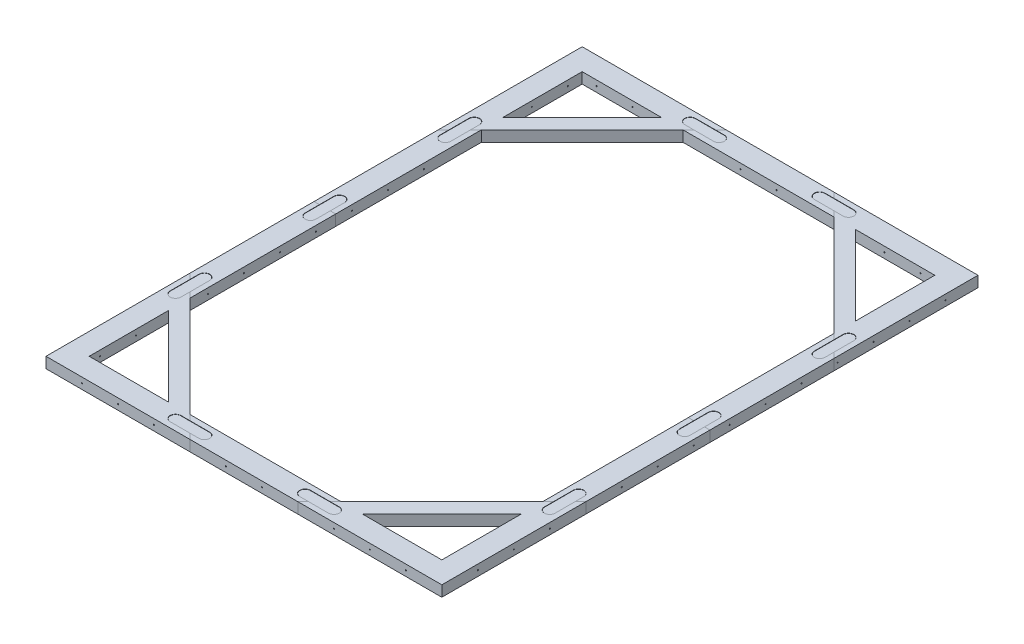
SolidWorks part; units mm, degrees
ref_plane "Front Plane" through (0, 0, 0) normal (0, 0, 1) x (1, 0, 0)
ref_plane "Top Plane" through (0, 0, 0) normal (0, 1, 0) x (1, 0, 0)
ref_plane "Right Plane" through (0, 0, 0) normal (1, 0, 0) x (0, 0, -1)
sketch "Sketch1" plane through (0, 0, 0) normal (0, 1, 0) x (1, 0, 0)
  line L0 (170, 715) -> (30, 575)
  line L1 (0, 0) -> (550, 0)
  line L2 (0, 0) -> (0, 745)
  line L3 (0, 745) -> (550, 745)
  line L4 (550, 0) -> (550, 745)
  line L5 (275, 745) -> (275, 0) construction
  line L6 (0, 372.5) -> (550, 372.5) construction
  line L7 (380, 715) -> (520, 575)
  line L8 (380, 30) -> (520, 170)
  line L9 (170, 30) -> (30, 170)
  line L10 (170, 715) -> (380, 715)
  line L11 (520, 170) -> (520, 575)
  line L12 (170, 30) -> (380, 30)
  line L13 (30, 170) -> (30, 575)
  line L15 (30, 715) -> (520, 715) construction
  line L16 (30, 30) -> (30, 715) construction
  line L17 (30, 30) -> (520, 30) construction
  line L18 (520, 30) -> (520, 715) construction
  dimension "D1" = 550
  dimension "D2" = 745
  dimension "D5" = 30
extrude "Boss-Extrude1" add sketch "Sketch1" along normal blind 15
sketch "Sketch2" plane through (0, 15, 0) normal (0, 1, 0) x (1, 0, 0)
  line L0 (140, 715) -> (30, 715)
  line L1 (30, 715) -> (30, 605)
  line L2 (30, 605) -> (140, 715)
  line L3 (380, 715) -> (170, 715) construction
  line L4 (30, 575) -> (30, 170) construction
  line L5 (170, 715) -> (30, 575) construction
  line L6 (275, 745) -> (275, 545.877) construction
  line L7 (550, 745) -> (0, 745) construction
  line L8 (520, 715) -> (520, 605)
  line L9 (410, 715) -> (520, 715)
  line L10 (520, 605) -> (410, 715)
  line L11 (0, 372.5) -> (324.6432, 372.5) construction
  line L12 (0, 745) -> (0, 0) construction
  line L13 (410, 30) -> (520, 30)
  line L14 (520, 140) -> (410, 30)
  line L15 (520, 30) -> (520, 140)
  line L16 (30, 30) -> (30, 140)
  line L17 (140, 30) -> (30, 30)
  line L18 (30, 140) -> (140, 30)
  dimension "D1" = 30
extrude "Cut-Extrude1" cut sketch "Sketch2" against normal blind 15
sketch "Sketch3" plane through (0, 15, 0) normal (0, 1, 0) x (1, 0, 0)
  line L0 (170, 715) -> (200, 745)
  line L1 (550, 745) -> (0, 745) construction
  line L2 (380, 715) -> (350, 745)
  line L3 (520, 575) -> (380, 715) construction
  line L4 (170, 715) -> (30, 575) construction
  line L5 (30, 575) -> (0, 545)
  line L6 (0, 745) -> (0, 0) construction
  line L7 (520, 575) -> (550, 545)
  line L8 (550, 0) -> (550, 745) construction
  line L9 (30, 170) -> (0, 200)
  line L10 (30, 170) -> (170, 30) construction
  line L11 (170, 30) -> (200, 0)
  line L12 (0, 0) -> (550, 0) construction
  line L13 (520, 170) -> (550, 200)
  line L14 (380, 30) -> (350, 0)
  line L15 (380, 30) -> (520, 170) construction
  line L16 (0, 372.5) -> (30, 372.5)
  line L17 (30, 575) -> (30, 170) construction
  line L18 (520, 372.5) -> (550, 372.5)
  line L19 (520, 170) -> (520, 575) construction
extrude "Cut-Extrude-Thin1" cut sketch "Sketch3" against normal blind 15 thin thin type mid plane wall 0.0001
sketch "Sketch4" plane through (0, 15, 0) normal (0, 1, 0) x (1, 0, 0)
  line L0 (184.9999, 730) -> (365.0001, 730) construction
  line L1 (170, 715) -> (199.9999, 745) construction
  line L2 (380, 715) -> (350.0001, 745) construction
  line L3 (164.9999, 730) -> (204.9999, 730) construction
  line L4 (164.9999, 737.5) -> (204.9999, 737.5)
  line L5 (164.9999, 722.5) -> (204.9999, 722.5)
  line L6 (275, 745) -> (275, 715) construction
  line L7 (350, 745) -> (200, 745) construction
  line L8 (379.9999, 715) -> (170.0001, 715) construction
  line L9 (385.0001, 730) -> (345.0001, 730) construction
  line L10 (385.0001, 737.5) -> (345.0001, 737.5)
  line L11 (385.0001, 722.5) -> (345.0001, 722.5)
  line L12 (0, 372.5) -> (550, 372.5) construction
  line L13 (385.0001, 14.9999) -> (345.0001, 14.9999) construction
  line L14 (385.0001, 7.4999) -> (345.0001, 7.4999)
  line L15 (385.0001, 22.4999) -> (345.0001, 22.4999)
  line L16 (164.9999, 14.9999) -> (204.9999, 14.9999) construction
  line L17 (164.9999, 7.4999) -> (204.9999, 7.4999)
  line L18 (164.9999, 22.4999) -> (204.9999, 22.4999)
  line L19 (15, 580.0001) -> (15, 540.0001) construction
  line L20 (22.5, 580.0001) -> (22.5, 540.0001)
  line L21 (7.5, 580.0001) -> (7.5, 540.0001)
  line L22 (30, 575) -> (0, 545.0001) construction
  line L23 (15, 164.9998) -> (15, 204.9998) construction
  line L24 (22.5, 164.9998) -> (22.5, 204.9998)
  line L25 (7.5, 164.9998) -> (7.5, 204.9998)
  line L26 (535, 580.0001) -> (535, 540.0001) construction
  line L27 (527.5, 580.0001) -> (527.5, 540.0001)
  line L28 (542.5, 580.0001) -> (542.5, 540.0001)
  line L29 (535, 164.9998) -> (535, 204.9998) construction
  line L30 (527.5, 164.9998) -> (527.5, 204.9998)
  line L31 (542.5, 164.9998) -> (542.5, 204.9998)
  line L32 (15, 392.5) -> (15, 352.5) construction
  line L33 (22.5, 392.5) -> (22.5, 352.5)
  line L34 (7.5, 392.5) -> (7.5, 352.5)
  line L35 (535, 392.5) -> (535, 352.5) construction
  line L36 (527.5, 392.5) -> (527.5, 352.5)
  line L37 (542.5, 392.5) -> (542.5, 352.5)
  arc A0 (164.9999, 737.5) -> (164.9999, 722.5) centre (164.9999, 730) ccw
  arc A1 (204.9999, 722.5) -> (204.9999, 737.5) centre (204.9999, 730) ccw
  arc A2 (385.0001, 737.5) -> (385.0001, 722.5) centre (385.0001, 730) cw
  arc A3 (345.0001, 722.5) -> (345.0001, 737.5) centre (345.0001, 730) cw
  arc A4 (385.0001, 7.4999) -> (385.0001, 22.4999) centre (385.0001, 14.9999) ccw
  arc A5 (345.0001, 22.4999) -> (345.0001, 7.4999) centre (345.0001, 14.9999) ccw
  arc A6 (164.9999, 7.4999) -> (164.9999, 22.4999) centre (164.9999, 14.9999) cw
  arc A7 (204.9999, 22.4999) -> (204.9999, 7.4999) centre (204.9999, 14.9999) cw
  arc A8 (22.5, 580.0001) -> (7.5, 580.0001) centre (15, 580.0001) ccw
  arc A9 (7.5, 540.0001) -> (22.5, 540.0001) centre (15, 540.0001) ccw
  arc A10 (22.5, 164.9998) -> (7.5, 164.9998) centre (15, 164.9998) cw
  arc A11 (7.5, 204.9998) -> (22.5, 204.9998) centre (15, 204.9998) cw
  arc A12 (527.5, 580.0001) -> (542.5, 580.0001) centre (535, 580.0001) cw
  arc A13 (542.5, 540.0001) -> (527.5, 540.0001) centre (535, 540.0001) cw
  arc A14 (527.5, 164.9998) -> (542.5, 164.9998) centre (535, 164.9998) ccw
  arc A15 (542.5, 204.9998) -> (527.5, 204.9998) centre (535, 204.9998) ccw
  arc A16 (22.5, 392.5) -> (7.5, 392.5) centre (15, 392.5) ccw
  arc A17 (7.5, 352.5) -> (22.5, 352.5) centre (15, 352.5) ccw
  arc A18 (527.5, 392.5) -> (542.5, 392.5) centre (535, 392.5) cw
  arc A19 (542.5, 352.5) -> (527.5, 352.5) centre (535, 352.5) cw
  point P8 (184.9999, 730)
  point P21 (365.0001, 730)
  point P32 (365.0001, 14.9999)
  point P39 (184.9999, 14.9999)
  point P46 (15, 560.0001)
  point P51 (15, 372.5)
  point P56 (15, 184.9998)
  point P63 (535, 560.0001)
  point P70 (535, 184.9998)
  point P84 (535, 372.5)
  dimension "D1" = 40
  dimension "D2" = 15
  dimension "D3" = 40
  dimension "D4" = 15
  dimension "D5" = 40
  dimension "D6" = 15
extrude "Cut-Extrude2" cut sketch "Sketch4" against normal blind 5
sketch "Sketch5" plane through (0, 10, 0) normal (0, 1, 0) x (1, 0, 0)
  line L20 (177.5, 22.2999) -> (164.9999, 22.2999)
  line L21 (164.9999, 22.2999) -> (204.9999, 22.2999)
  line L26 (164.9999, 7.6999) -> (204.9999, 7.6999)
  line L27 (192.5002, 7.6999) -> (204.9999, 7.6999)
  line L28 (204.9999, 22.2999) -> (177.5002, 22.2999)
  line L29 (7.7, 392.5) -> (7.7, 352.5)
  line L30 (22.3, 392.5) -> (22.3, 352.5)
  line L31 (22.3, 204.9998) -> (22.3, 164.9998)
  line L32 (7.7, 204.9998) -> (7.7, 164.9998)
  line L33 (275, 715) -> (275, 30) construction
  line L34 (379.9999, 715) -> (170.0001, 715) construction
  line L35 (170.0001, 30) -> (379.9999, 30) construction
  line L36 (30, 372.5001) -> (520, 372.5) construction
  line L37 (542.3, 392.5) -> (542.3, 352.5)
  line L38 (527.7, 392.5) -> (527.7, 352.5)
  line L39 (542.3, 204.9998) -> (542.3, 164.9998)
  line L40 (527.7, 204.9998) -> (527.7, 164.9998)
  line L41 (385.0001, 22.2999) -> (345.0001, 22.2999)
  line L42 (385.0001, 7.6999) -> (345.0001, 7.6999)
  line L43 (542.3001, 540) -> (542.3001, 580)
  line L44 (527.7001, 540) -> (527.7001, 580)
  line L45 (7.7001, 540.0003) -> (7.7001, 580.0003)
  line L46 (22.3001, 540.0003) -> (22.3001, 580.0003)
  line L47 (165.0001, 722.7002) -> (205.0001, 722.7001)
  line L48 (165.0001, 737.3002) -> (205.0001, 737.3001)
  line L49 (385.0002, 737.3001) -> (345.0002, 737.3001)
  line L50 (385.0002, 722.7001) -> (345.0002, 722.7001)
  arc A10 (164.9999, 22.2999) -> (164.9999, 7.6999) centre (164.9999, 14.9999) ccw
  arc A11 (164.9999, 22.2999) -> (164.9999, 7.6999) centre (164.9999, 14.9999) ccw
  arc A14 (204.9999, 7.6999) -> (204.9999, 22.2999) centre (204.9999, 14.9999) ccw
  arc A15 (204.9999, 7.6999) -> (204.9999, 22.2999) centre (204.9999, 14.9999) ccw
  arc A17 (22.3, 204.9998) -> (7.7, 204.9998) centre (15, 204.9998) ccw
  arc A18 (22.3, 204.9998) -> (7.7, 204.9998) centre (15, 204.9998) ccw
  arc A20 (7.7, 164.9998) -> (22.3, 164.9998) centre (15, 164.9998) ccw
  arc A21 (7.7, 164.9998) -> (22.3, 164.9998) centre (15, 164.9998) ccw
  arc A23 (22.3, 392.5) -> (7.7, 392.5) centre (15, 392.5) ccw
  arc A24 (22.3, 392.5) -> (7.7, 392.5) centre (15, 392.5) ccw
  arc A25 (542.3, 352.5) -> (527.7, 352.5) centre (535, 352.5) cw
  arc A26 (7.7, 352.5) -> (22.3, 352.5) centre (15, 352.5) ccw
  arc A27 (7.7, 352.5) -> (22.3, 352.5) centre (15, 352.5) ccw
  arc A28 (527.7, 392.5) -> (542.3, 392.5) centre (535, 392.5) cw
  arc A29 (542.3, 164.9998) -> (527.7, 164.9998) centre (535, 164.9998) cw
  arc A30 (527.7, 204.9998) -> (542.3, 204.9998) centre (535, 204.9998) cw
  arc A31 (345.0001, 7.6999) -> (345.0001, 22.2999) centre (345.0001, 14.9999) cw
  arc A32 (385.0001, 22.2999) -> (385.0001, 7.6999) centre (385.0001, 14.9999) cw
  arc A33 (527.7001, 540) -> (542.3001, 540) centre (535.0001, 540) ccw
  arc A34 (542.3001, 580) -> (527.7001, 580) centre (535.0001, 580) ccw
  arc A35 (7.7001, 580.0003) -> (22.3001, 580.0003) centre (15.0001, 580.0003) cw
  arc A36 (22.3001, 540.0003) -> (7.7001, 540.0003) centre (15.0001, 540.0003) cw
  arc A37 (205.0001, 737.3001) -> (205.0001, 722.7001) centre (205.0001, 730.0001) cw
  arc A38 (165.0001, 722.7002) -> (165.0001, 737.3002) centre (165.0001, 730.0002) cw
  arc A39 (385.0002, 722.7001) -> (385.0002, 737.3001) centre (385.0002, 730.0001) ccw
  arc A40 (345.0002, 737.3001) -> (345.0002, 722.7001) centre (345.0002, 730.0001) ccw
  dimension "D1" = 0.2
  dimension "D2" = 0.2
  dimension "D3" = 0.2
  dimension "D4" = 0.2
  dimension "D5" = 0.2
  dimension "D6" = 0.2
extrude "Boss-Extrude2" add sketch "Sketch5" along normal blind 4.8 separate body
sketch "Sketch8" plane through (0, 0, 0) normal (0, 0, 1) x (1, 0, 0)
  line L0 (0, 7.5) -> (550, 7.5) construction
  line L1 (0, 15) -> (0, 0) construction
  line L2 (550, 15) -> (550, 0) construction
  circle A0 centre (50, 7.5) radius 0.75
  circle A1 centre (100, 7.5) radius 0.75
  circle A2 centre (150, 7.5) radius 0.75
  circle A4 centre (250, 7.5) radius 0.75
  circle A5 centre (300, 7.5) radius 0.75
  circle A7 centre (400, 7.5) radius 0.75
  circle A8 centre (450, 7.5) radius 0.75
  circle A9 centre (500, 7.5) radius 0.75
  circle A10 centre (200, 7.5) radius 0.75 [skipped]
  circle A11 centre (350, 7.5) radius 0.75 [skipped]
  dimension "D1" = 1.5
  dimension "D2" = 50
  dimension "D3" = 10
extrude "Cut-Extrude3" cut sketch "Sketch8" against normal up to surface (30 mm away) up to face at (85, 7.5, -30)
sketch "Sketch9" plane through (550, 0, 0) normal (1, 0, 0) x (0, 0, -1)
  line L0 (0, 7.5) -> (745, 7.5) construction
  line L1 (0, 15) -> (0, 0) construction
  line L2 (745, 15) -> (745, 0) construction
  circle A0 centre (50, 7.5) radius 0.75
  circle A1 centre (100, 7.5) radius 0.75
  circle A2 centre (150, 7.5) radius 0.75
  circle A4 centre (250, 7.5) radius 0.75
  circle A5 centre (300, 7.5) radius 0.75
  circle A6 centre (350, 7.5) radius 0.75
  circle A7 centre (400, 7.5) radius 0.75
  circle A8 centre (450, 7.5) radius 0.75
  circle A9 centre (500, 7.5) radius 0.75
  circle A10 centre (550, 7.5) radius 0.75
  circle A11 centre (600, 7.5) radius 0.75
  circle A12 centre (650, 7.5) radius 0.75
  circle A13 centre (700, 7.5) radius 0.75
  circle A14 centre (200, 7.5) radius 0.75 [skipped]
  dimension "D1" = 1.5
  dimension "D2" = 50
  dimension "D3" = 14
extrude "Cut-Extrude4" cut sketch "Sketch9" against normal up to surface (30 mm away) up to face at (520, 7.5, -271.25)
sketch "Sketch10" plane through (0, 0, -745) normal (0, 0, -1) x (-1, 0, 0)
  line L0 (-550, 7.5) -> (0, 7.5) construction
  line L1 (-550, 15) -> (-550, 0) construction
  line L2 (0, 15) -> (0, 0) construction
  circle A0 centre (-500, 7.5) radius 0.75
  circle A1 centre (-450, 7.5) radius 0.75
  circle A2 centre (-400, 7.5) radius 0.75
  circle A4 centre (-300, 7.5) radius 0.75
  circle A5 centre (-250, 7.5) radius 0.75
  circle A7 centre (-150, 7.5) radius 0.75
  circle A8 centre (-100, 7.5) radius 0.75
  circle A9 centre (-50, 7.5) radius 0.75
  circle A10 centre (-350, 7.5) radius 0.75 [skipped]
  circle A11 centre (-200, 7.5) radius 0.75 [skipped]
  dimension "D1" = 1.5
  dimension "D2" = 50
  dimension "D3" = 10
extrude "Cut-Extrude5" cut sketch "Sketch10" against normal up to surface (30 mm away) up to face at (275, 7.5, -715)
sketch "Sketch11" plane through (0, 0, 0) normal (-1, 0, 0) x (0, 0, 1)
  line L0 (-745, 7.5) -> (0, 7.5) construction
  line L1 (-745, 15) -> (-745, 0) construction
  line L2 (0, 15) -> (0, 0) construction
  circle A0 centre (-695, 7.5) radius 0.75
  circle A1 centre (-645, 7.5) radius 0.75
  circle A2 centre (-595, 7.5) radius 0.75
  circle A4 centre (-495, 7.5) radius 0.75
  circle A5 centre (-445, 7.5) radius 0.75
  circle A6 centre (-395, 7.5) radius 0.75
  circle A7 centre (-345, 7.5) radius 0.75
  circle A8 centre (-295, 7.5) radius 0.75
  circle A9 centre (-245, 7.5) radius 0.75
  circle A10 centre (-195, 7.5) radius 0.75
  circle A11 centre (-145, 7.5) radius 0.75
  circle A12 centre (-95, 7.5) radius 0.75
  circle A13 centre (-45, 7.5) radius 0.75
  circle A14 centre (-545, 7.5) radius 0.75 [skipped]
  dimension "D1" = 1.5
  dimension "D2" = 50
  dimension "D3" = 14
extrude "Cut-Extrude6" cut sketch "Sketch11" against normal up to surface (30 mm away) up to face at (30, 7.5, -473.75)
